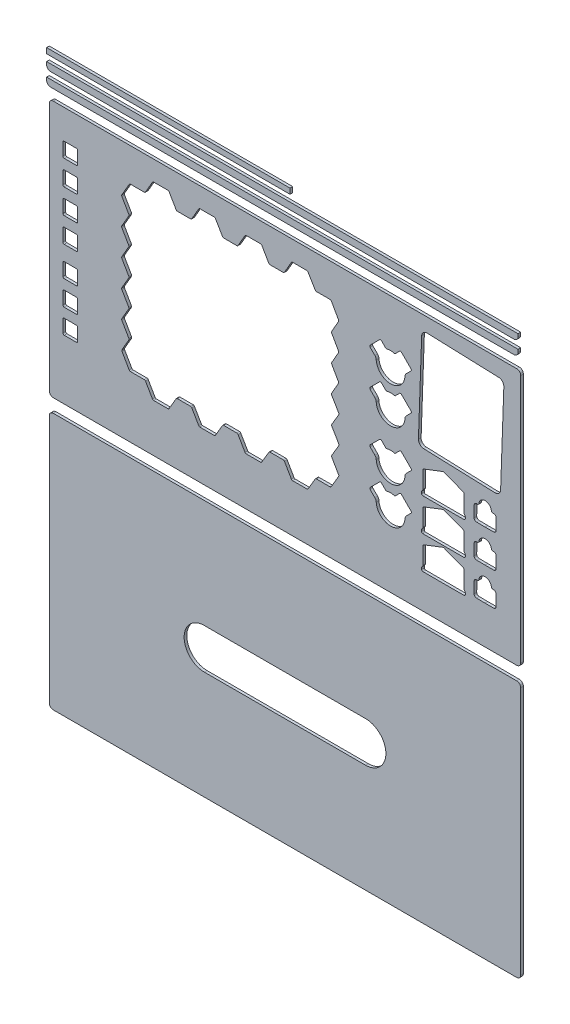
SolidWorks part; units mm, degrees
other "个人版图-顶面"
other "个人版图_长边框"
other "个人版图-长边框2"
other "个人版图-短边框"
other "个人版图-底面"
ref_plane "前视基准面" through (0, 0, 0) normal (0, 0, 1) x (1, 0, 0)
ref_plane "上视基准面" through (0, 0, 0) normal (0, 1, 0) x (1, 0, 0)
ref_plane "右视基准面" through (0, 0, 0) normal (1, 0, 0) x (0, 0, -1)
sketch "草图1"
  line L0 (0, -0.5) -> (340.5, -0.5) construction
  line L1 (0, 0) -> (340, 0) construction
  line L2 (0, 0) -> (0, 180) construction
  line L3 (0, 180) -> (340, 180) construction
  line L4 (340, 0) -> (340, 180) construction
  line L5 (340.5, -0.5) -> (340.5, 180.5) construction
  line L6 (0, 180.5) -> (340.5, 180.5) construction
  line L7 (0, 180.5) -> (0, -0.5) construction
  line L8 (-5, 185.5) -> (-5, -5.5)
  line L9 (-5, -5.5) -> (345.5, -5.5)
  line L10 (345.5, -5.5) -> (345.5, 185.5)
  line L11 (-5, 185.5) -> (345.5, 185.5)
  line L12 (72.0083, 170.7) -> (83.7745, 170.7)
  line L13 (72.0083, 170.7) -> (66.2258, 160.6844)
  line L14 (54.7313, 160.6844) -> (66.2258, 160.6844)
  line L15 (54.7313, 160.6844) -> (48.6498, 150.1509)
  line L16 (48.6498, 150.1509) -> (54.4143, 140.1664)
  line L17 (54.4143, 140.1664) -> (48.6, 130.0957)
  line L18 (48.6, 130.0957) -> (54.3252, 120.1794)
  line L19 (54.3252, 120.1794) -> (48.6138, 110.287)
  line L20 (48.6138, 110.287) -> (54.3978, 100.2686)
  line L21 (54.3978, 100.2686) -> (48.6138, 90.2503)
  line L22 (48.6138, 90.2503) -> (54.3644, 80.2899)
  line L23 (54.3644, 80.2899) -> (48.6422, 70.3787)
  line L24 (48.6422, 70.3787) -> (54.4413, 60.3343)
  line L25 (54.4413, 60.3343) -> (48.7277, 50.4381)
  line L26 (48.7277, 50.4381) -> (54.7313, 40.0396)
  line L27 (54.7313, 40.0396) -> (66.2258, 40.0396)
  line L28 (66.2258, 40.0396) -> (72.0083, 30.0711)
  line L29 (72.0083, 30.0711) -> (83.7745, 30.0711)
  line L30 (83.7745, 30.0711) -> (89.6163, 40.0396)
  line L31 (89.6163, 40.0396) -> (100.6288, 40.0396)
  line L32 (100.6288, 40.0396) -> (106.4113, 30.0711)
  line L33 (106.4113, 30.0711) -> (118.2358, 30.0711)
  line L34 (118.2358, 30.0711) -> (124.0775, 40.0396)
  line L35 (124.0775, 40.0396) -> (135.0409, 40.0396)
  line L36 (135.0409, 40.0396) -> (140.8234, 30.0711)
  line L37 (140.8234, 30.0711) -> (152.6864, 30.0711)
  line L38 (152.6864, 30.0711) -> (158.5281, 40.0396)
  line L39 (158.5281, 40.0396) -> (169.5234, 40.0396)
  line L40 (169.5234, 40.0396) -> (175.3059, 30.0711)
  line L41 (175.3059, 30.0711) -> (187.1478, 30.0711)
  line L42 (187.1478, 30.0711) -> (192.9895, 40.0396)
  line L43 (192.9895, 40.0396) -> (204.3316, 40.0396)
  line L44 (204.3316, 40.0396) -> (210.4252, 50.4381)
  line L45 (210.4252, 50.4381) -> (204.6847, 60.3343)
  line L46 (204.6847, 60.3343) -> (210.5708, 70.3787)
  line L47 (210.5708, 70.3787) -> (204.6847, 80.2899)
  line L48 (204.6847, 80.2899) -> (210.5216, 90.2503)
  line L49 (210.5216, 90.2503) -> (204.5718, 100.2686)
  line L50 (204.5718, 100.2686) -> (210.2931, 110.287)
  line L51 (210.2931, 110.287) -> (204.6847, 120.1794)
  line L52 (204.6847, 120.1794) -> (210.3476, 130.0957)
  line L53 (210.3476, 130.0957) -> (204.6381, 140.1664)
  line L54 (204.6381, 140.1664) -> (210.3476, 150.1641)
  line L55 (210.3476, 150.1641) -> (204.3833, 160.6844)
  line L56 (204.3833, 160.6844) -> (192.9895, 160.6844)
  line L57 (192.9895, 160.6844) -> (187.0413, 170.7)
  line L58 (152.6864, 170.7) -> (158.5281, 160.6844)
  line L59 (158.5281, 160.6844) -> (169.5234, 160.6844)
  line L60 (169.5234, 160.6844) -> (175.3059, 170.7)
  line L61 (118.2358, 170.7) -> (124.0775, 160.6844)
  line L62 (124.0775, 160.6844) -> (135.0409, 160.6844)
  line L63 (135.0409, 160.6844) -> (140.8234, 170.7)
  line L64 (83.7745, 170.7) -> (89.6163, 160.6844)
  line L65 (89.6163, 160.6844) -> (100.6288, 160.6844)
  line L66 (100.6288, 160.6844) -> (106.4113, 170.7)
  line L67 (106.4113, 170.7) -> (118.2358, 170.7)
  line L68 (140.8234, 170.7) -> (152.6864, 170.7)
  line L69 (175.3059, 170.7) -> (187.0413, 170.7)
  line L70 (5.1103, 163.713) -> (16.1103, 163.713)
  line L71 (6.1103, 162.713) -> (15.1103, 162.713) construction
  line L72 (6.1103, 162.713) -> (6.1103, 153.713) construction
  line L73 (6.1103, 153.713) -> (15.1103, 153.713) construction
  line L74 (15.1103, 162.713) -> (15.1103, 153.713) construction
  line L75 (16.1103, 163.713) -> (16.1103, 152.713)
  line L76 (5.1103, 152.713) -> (16.1103, 152.713)
  line L77 (5.1103, 163.713) -> (5.1103, 152.713)
  line L78 (5.1103, 134.263) -> (16.1103, 134.263)
  line L79 (16.1103, 145.263) -> (16.1103, 134.263)
  line L80 (5.1103, 145.263) -> (16.1103, 145.263)
  line L81 (5.1103, 145.263) -> (5.1103, 134.263)
  line L82 (5.1103, 115.813) -> (16.1103, 115.813)
  line L83 (16.1103, 126.813) -> (16.1103, 115.813)
  line L84 (5.1103, 126.813) -> (16.1103, 126.813)
  line L85 (5.1103, 126.813) -> (5.1103, 115.813)
  line L86 (5.1103, 97.363) -> (16.1103, 97.363)
  line L87 (16.1103, 108.363) -> (16.1103, 97.363)
  line L88 (5.1103, 108.363) -> (16.1103, 108.363)
  line L89 (5.1103, 108.363) -> (5.1103, 97.363)
  line L90 (5.1103, 75.2175) -> (16.1103, 75.2175)
  line L91 (16.1103, 86.2175) -> (16.1103, 75.2175)
  line L92 (5.1103, 86.2175) -> (16.1103, 86.2175)
  line L93 (5.1103, 86.2175) -> (5.1103, 75.2175)
  line L94 (5.1103, 56.8589) -> (16.1103, 56.8589)
  line L95 (16.1103, 67.8589) -> (16.1103, 56.8589)
  line L96 (5.1103, 67.8589) -> (16.1103, 67.8589)
  line L97 (5.1103, 67.8589) -> (5.1103, 56.8589)
  line L98 (5.1103, 38.7973) -> (16.1103, 38.7973)
  line L99 (16.1103, 49.7973) -> (16.1103, 38.7973)
  line L100 (5.1103, 49.7973) -> (16.1103, 49.7973)
  line L101 (5.1103, 49.7973) -> (5.1103, 38.7973)
  line L102 (264.6336, 145.4227) -> (256.14, 153.9163)
  line L103 (256.14, 153.9163) -> (251.9519, 149.7283)
  line L104 (245.4671, 149.7283) -> (241.2907, 153.9046)
  line L105 (241.2907, 153.9046) -> (232.8691, 145.483)
  line L106 (232.8691, 145.483) -> (237.0658, 141.2863)
  line L107 (264.6336, 145.4227) -> (260.4972, 141.2863)
  line L108 (264.6336, 81.2459) -> (256.14, 89.7395)
  line L109 (256.14, 89.7395) -> (251.9519, 85.5515)
  line L110 (245.4671, 85.5515) -> (241.2907, 89.7278)
  line L111 (241.2907, 89.7278) -> (232.8691, 81.3062)
  line L112 (232.8691, 81.3062) -> (237.0658, 77.1095)
  line L113 (264.6336, 81.2459) -> (260.4972, 77.1095)
  line L114 (264.6336, 118.3025) -> (256.14, 126.7961)
  line L115 (256.14, 126.7961) -> (251.9519, 122.6081)
  line L116 (245.4671, 122.6081) -> (241.2907, 126.7844)
  line L117 (241.2907, 126.7844) -> (232.8691, 118.3628)
  line L118 (232.8691, 118.3628) -> (237.0658, 114.1661)
  line L119 (264.6336, 118.3025) -> (260.4972, 114.1661)
  line L120 (264.6336, 53.8293) -> (256.14, 62.3229)
  line L121 (256.14, 62.3229) -> (251.9519, 58.1349)
  line L122 (245.4671, 58.1349) -> (241.2907, 62.3112)
  line L123 (241.2907, 62.3112) -> (232.8691, 53.8896)
  line L124 (232.8691, 53.8896) -> (237.0658, 49.6929)
  line L125 (264.6336, 53.8293) -> (260.4972, 49.6929)
  line L126 (272.2895, 20.4596) -> (272.2895, 22.3194) construction
  line L127 (272.2895, 22.3194) -> (273.2488, 23.5312) construction
  line L128 (273.2488, 23.5312) -> (273.2488, 36.9443) construction
  line L129 (273.2488, 36.9443) -> (288.0439, 42.643) construction
  line L130 (272.2895, 20.4596) -> (303.7983, 20.4596) construction
  line L131 (288.0439, 42.643) -> (288.0439, 20.4596) construction
  line L132 (302.839, 36.9443) -> (288.0439, 42.643) construction
  line L133 (302.839, 23.5312) -> (302.839, 36.9443) construction
  line L134 (303.7983, 22.3194) -> (302.839, 23.5312) construction
  line L135 (303.7983, 20.4596) -> (303.7983, 22.3194) construction
  line L136 (303.339, 37.2876) -> (288.0439, 43.1788)
  line L137 (272.7488, 37.2876) -> (288.0439, 43.1788)
  line L138 (272.7488, 23.7052) -> (272.7488, 37.2876)
  line L139 (271.7895, 22.4934) -> (272.7488, 23.7052)
  line L140 (271.7895, 19.9596) -> (271.7895, 22.4934)
  line L141 (271.7895, 19.9596) -> (304.2983, 19.9596)
  line L142 (304.2983, 19.9596) -> (304.2983, 22.4934)
  line L143 (304.2983, 22.4934) -> (303.339, 23.7052)
  line L144 (303.339, 23.7052) -> (303.339, 37.2876)
  line L145 (272.7488, 61.6876) -> (288.0439, 67.5788)
  line L146 (303.339, 61.6876) -> (288.0439, 67.5788)
  line L147 (303.339, 48.1052) -> (303.339, 61.6876)
  line L148 (304.2983, 46.8934) -> (303.339, 48.1052)
  line L149 (304.2983, 44.3596) -> (304.2983, 46.8934)
  line L150 (271.7895, 44.3596) -> (304.2983, 44.3596)
  line L151 (271.7895, 44.3596) -> (271.7895, 46.8934)
  line L152 (271.7895, 46.8934) -> (272.7488, 48.1052)
  line L153 (272.7488, 48.1052) -> (272.7488, 61.6876)
  line L154 (272.7488, 86.0876) -> (288.0439, 91.9788)
  line L155 (303.339, 86.0876) -> (288.0439, 91.9788)
  line L156 (303.339, 72.5052) -> (303.339, 86.0876)
  line L157 (304.2983, 71.2934) -> (303.339, 72.5052)
  line L158 (304.2983, 68.7596) -> (304.2983, 71.2934)
  line L159 (271.7895, 68.7596) -> (304.2983, 68.7596)
  line L160 (271.7895, 68.7596) -> (271.7895, 71.2934)
  line L161 (271.7895, 71.2934) -> (272.7488, 72.5052)
  line L162 (272.7488, 72.5052) -> (272.7488, 86.0876)
  line L163 (319.0697, 88.7733) -> (318.9881, 71.7735) construction
  line L164 (318.9881, 71.7735) -> (325.3925, 71.7735)
  line L165 (327.1925, 73.5735) -> (327.1925, 81.8155)
  line L166 (325.3925, 83.6155) -> (323.6584, 83.6155)
  line L167 (318.9881, 71.7735) -> (312.584, 71.835)
  line L168 (310.8014, 73.6522) -> (310.8806, 81.8939)
  line L169 (312.6978, 83.6765) -> (314.4318, 83.6598)
  line L170 (325.3925, 59.1155) -> (323.6584, 59.1155)
  line L171 (327.1925, 49.0735) -> (327.1925, 57.3155)
  line L172 (318.9881, 47.2735) -> (325.3925, 47.2735)
  line L173 (318.9881, 47.2735) -> (312.584, 47.335)
  line L174 (310.8014, 49.1522) -> (310.8806, 57.3939)
  line L175 (312.6978, 59.1765) -> (314.4318, 59.1598)
  line L176 (325.3925, 34.6155) -> (323.6584, 34.6155)
  line L177 (327.1925, 24.5735) -> (327.1925, 32.8155)
  line L178 (318.9881, 22.7735) -> (325.3925, 22.7735)
  line L179 (318.9881, 22.7735) -> (312.584, 22.835)
  line L180 (310.8014, 24.6522) -> (310.8806, 32.8939)
  line L181 (312.6978, 34.6765) -> (314.4318, 34.6598)
  line L182 (271.9931, 175.2345) -> (333.0932, 173.0732)
  line L183 (333.0932, 173.0732) -> (330.4164, 97.398)
  line L184 (330.4164, 97.398) -> (269.3163, 99.5593)
  line L185 (269.3163, 99.5593) -> (271.9931, 175.2345)
  arc A0 (245.4671, 149.7283) -> (251.9519, 149.7283) centre (248.7095, 139.9876) cw
  arc A1 (237.0658, 141.2863) -> (238.0695, 138.8627) centre (234.6427, 138.8631) cw
  arc A2 (238.0695, 138.8627) -> (259.4313, 138.8627) centre (248.7504, 139.5892) ccw
  arc A3 (260.4972, 141.2863) -> (259.4313, 138.8627) centre (263.0786, 138.7048) ccw
  arc A4 (245.4671, 85.5515) -> (251.9519, 85.5515) centre (248.7095, 75.8108) cw
  arc A5 (237.0658, 77.1095) -> (238.0695, 74.6859) centre (234.6427, 74.6864) cw
  arc A6 (238.0695, 74.6859) -> (259.4313, 74.6859) centre (248.7504, 75.4124) ccw
  arc A7 (260.4972, 77.1095) -> (259.4313, 74.6859) centre (263.0786, 74.5281) ccw
  arc A8 (245.4671, 122.6081) -> (251.9519, 122.6081) centre (248.7095, 112.8674) cw
  arc A9 (237.0658, 114.1661) -> (238.0695, 111.7425) centre (234.6427, 111.743) cw
  arc A10 (238.0695, 111.7425) -> (259.4313, 111.7425) centre (248.7504, 112.469) ccw
  arc A11 (260.4972, 114.1661) -> (259.4313, 111.7425) centre (263.0786, 111.5847) ccw
  arc A12 (245.4671, 58.1349) -> (251.9519, 58.1349) centre (248.7095, 48.3942) cw
  arc A13 (237.0658, 49.6929) -> (238.0695, 47.2693) centre (234.6427, 47.2698) cw
  arc A14 (238.0695, 47.2693) -> (259.4313, 47.2693) centre (248.7504, 47.9958) ccw
  arc A15 (260.4972, 49.6929) -> (259.4313, 47.2693) centre (263.0786, 47.1114) ccw
  arc A16 (314.4318, 83.6598) -> (323.6584, 83.6155) centre (319.0475, 84.1335) cw
  arc A17 (325.3925, 71.7735) -> (327.1925, 73.5735) centre (325.3925, 73.5735) ccw
  arc A18 (327.1925, 81.8155) -> (325.3925, 83.6155) centre (325.3925, 81.8155) ccw
  arc A19 (312.584, 71.835) -> (310.8014, 73.6522) centre (312.6013, 73.635) cw
  arc A20 (310.8806, 81.8939) -> (312.6978, 83.6765) centre (312.6805, 81.8766) cw
  arc A21 (314.4318, 59.1598) -> (323.6584, 59.1155) centre (319.0475, 59.6335) cw
  arc A22 (327.1925, 57.3155) -> (325.3925, 59.1155) centre (325.3925, 57.3155) ccw
  arc A23 (325.3925, 47.2735) -> (327.1925, 49.0735) centre (325.3925, 49.0735) ccw
  arc A24 (312.584, 47.335) -> (310.8014, 49.1522) centre (312.6013, 49.135) cw
  arc A25 (310.8806, 57.3939) -> (312.6978, 59.1765) centre (312.6805, 57.3766) cw
  arc A26 (314.4318, 34.6598) -> (323.6584, 34.6155) centre (319.0475, 35.1335) cw
  arc A27 (327.1925, 32.8155) -> (325.3925, 34.6155) centre (325.3925, 32.8155) ccw
  arc A28 (325.3925, 22.7735) -> (327.1925, 24.5735) centre (325.3925, 24.5735) ccw
  arc A29 (312.584, 22.835) -> (310.8014, 24.6522) centre (312.6013, 24.635) cw
  arc A30 (310.8806, 32.8939) -> (312.6978, 34.6765) centre (312.6805, 32.8766) cw
  point P249 (269.3163, 99.5593)
  dimension "D15" = 1.8
  dimension "D1" = 340
  dimension "D2" = 180
  dimension "D5" = 9.3
  dimension "D6" = 120
  dimension "D7" = 120
  dimension "D8" = 120
  dimension "D9" = 48.6
  dimension "D10" = 9
  dimension "D13" = 0.5
  dimension "D3" = 0.5
  dimension "D4" = 5
  dimension "D11" = 1
  dimension "D12" = 4
  dimension "D14" = 3
  dimension "D16" = 3
extrude "凸台-拉伸1" add sketch "草图1" against normal blind 2
fillet "圆角1" radius 3 4 edges at (-5, -5.5, -1) (-5, 185.5, -1) (345.5, -5.5, -1) (345.5, 185.5, -1)
fillet "圆角2" radius 1 58 edges at (83.7745, 170.7, -1) (89.6163, 160.6844, -1) (100.6288, 160.6844, -1) (106.4113, 170.7, -1) (118.2358, 170.7, -1) (124.0775, 160.6844, -1) (135.0409, 160.6844, -1) (140.8234, 170.7, -1) (152.6864, 170.7, -1) (158.5281, 160.6844, -1) (169.5234, 160.6844, -1) (175.3059, 170.7, -1) (187.0413, 170.7, -1) (192.9895, 160.6844, -1) (204.3833, 160.6844, -1) (210.3476, 150.1641, -1) (204.6381, 140.1664, -1) (210.3476, 130.0957, -1) (204.6847, 120.1794, -1) (210.2931, 110.287, -1) (204.5718, 100.2686, -1) (210.5216, 90.2503, -1) (204.6847, 80.2899, -1) (210.5708, 70.3787, -1) (204.6847, 60.3343, -1) (210.4252, 50.4381, -1) (204.3316, 40.0396, -1) (192.9895, 40.0396, -1) (187.1478, 30.0711, -1) (175.3059, 30.0711, -1) (169.5234, 40.0396, -1) (158.5281, 40.0396, -1) (152.6864, 30.0711, -1) (140.8234, 30.0711, -1) (135.0409, 40.0396, -1) (124.0775, 40.0396, -1) (118.2358, 30.0711, -1) (106.4113, 30.0711, -1) (100.6288, 40.0396, -1) (89.6163, 40.0396, -1) (83.7745, 30.0711, -1) (72.0083, 30.0711, -1) (66.2258, 40.0396, -1) (54.7313, 40.0396, -1) (48.7277, 50.4381, -1) (54.4413, 60.3343, -1) (48.6422, 70.3787, -1) (54.3644, 80.2899, -1) (48.6138, 90.2503, -1) (54.3978, 100.2686, -1) (48.6138, 110.287, -1) (54.3252, 120.1794, -1) (48.6, 130.0957, -1) (54.4143, 140.1664, -1) (48.6498, 150.1509, -1) (54.7313, 160.6844, -1) (72.0083, 170.7, -1) (66.2258, 160.6844, -1)
fillet "圆角3" radius 1 96 edges at (16.1103, 163.713, -1) (5.1103, 152.713, -1) (5.1103, 163.713, -1) (16.1103, 86.2175, -1) (16.1103, 75.2175, -1) (5.1103, 75.2175, -1) (5.1103, 86.2175, -1) (16.1103, 145.263, -1) (16.1103, 134.263, -1) (5.1103, 134.263, -1) (5.1103, 145.263, -1) (16.1103, 126.813, -1) (16.1103, 115.813, -1) (5.1103, 115.813, -1) (5.1103, 126.813, -1) (16.1103, 108.363, -1) (16.1103, 97.363, -1) (5.1103, 97.363, -1) (5.1103, 108.363, -1) (16.1103, 67.8589, -1) (16.1103, 56.8589, -1) (5.1103, 56.8589, -1) (5.1103, 67.8589, -1) (16.1103, 49.7973, -1) (16.1103, 38.7973, -1) (5.1103, 38.7973, -1) (5.1103, 49.7973, -1) (259.4313, 138.8627, -1) (238.0695, 138.8627, -1) (232.8691, 145.483, -1) (241.2907, 153.9046, -1) (245.4671, 149.7283, -1) (251.9519, 149.7283, -1) (256.14, 153.9163, -1) (264.6336, 145.4227, -1) (259.4313, 74.6859, -1) (238.0695, 74.6859, -1) (232.8691, 81.3062, -1) (241.2907, 89.7278, -1) (245.4671, 85.5515, -1) (251.9519, 85.5515, -1) (256.14, 89.7395, -1) (264.6336, 81.2459, -1) (259.4313, 111.7425, -1) (238.0695, 111.7425, -1) (232.8691, 118.3628, -1) (241.2907, 126.7844, -1) (245.4671, 122.6081, -1) (251.9519, 122.6081, -1) (256.14, 126.7961, -1) (264.6336, 118.3025, -1) (259.4313, 47.2693, -1) (238.0695, 47.2693, -1) (232.8691, 53.8896, -1) (241.2907, 62.3112, -1) (245.4671, 58.1349, -1) (251.9519, 58.1349, -1) (256.14, 62.3229, -1) (264.6336, 53.8293, -1) (318.9881, 71.7735, -1) (314.4318, 83.6598, -1) (323.6584, 83.6155, -1) (304.2983, 46.8934, -1) (304.2983, 44.3596, -1) (271.7895, 44.3596, -1) (271.7895, 46.8934, -1) (272.7488, 48.1052, -1) (272.7488, 61.6876, -1) (288.0439, 67.5788, -1) (303.339, 61.6876, -1) (303.339, 48.1052, -1) (304.2983, 22.4934, -1) (304.2983, 19.9596, -1) (271.7895, 19.9596, -1) (271.7895, 22.4934, -1) (272.7488, 23.7052, -1) (272.7488, 37.2876, -1) (288.0439, 43.1788, -1) (303.339, 37.2876, -1) (303.339, 23.7052, -1) (304.2983, 71.2934, -1) (304.2983, 68.7596, -1) (271.7895, 68.7596, -1) (271.7895, 71.2934, -1) (272.7488, 72.5052, -1) (272.7488, 86.0876, -1) (288.0439, 91.9788, -1) (303.339, 86.0876, -1) (303.339, 72.5052, -1) (318.9881, 47.2735, -1) (314.4318, 59.1598, -1) (323.6584, 59.1155, -1) (318.9881, 22.7735, -1) (314.4318, 34.6598, -1) (323.6584, 34.6155, -1) (16.1103, 152.713, -1)
sketch "草图3" plane through (0, 0, 0) normal (0, 0, 1) x (1, 0, 0)
  line L0 (-5, 182.5) -> (-5, -2.5) construction
  line L1 (-5, 195.5) -> (345.5, 195.5)
  line L2 (-5, 195.5) -> (-5, 200.5)
  line L3 (-5, 200.5) -> (345.5, 200.5)
  line L4 (345.5, 195.5) -> (345.5, 200.5)
  line L5 (345.5, -2.5) -> (345.5, 182.5) construction
  line L6 (342.5, 185.5) -> (-2, 185.5) construction
  dimension "D1" = 5
  dimension "D2" = 10
extrude "凸台-拉伸2" add sketch "草图3" along normal blind 2 separate body
fillet "圆角4" radius 3 2 edges at (345.5, 195.5, 1) (-5, 195.5, 1)
pattern_linear "阵列(线性)1" count 2 spacing 10 along (0, 1, 0) of bodies 107
sketch "草图6" plane through (0, 0, 0) normal (0, 0, 1) x (1, 0, 0)
  line L0 (345.5, 210.5) -> (-5, 210.5) construction
  line L1 (-5, 215.5) -> (176, 215.5)
  line L2 (-5, 215.5) -> (-5, 219.5)
  line L3 (-5, 219.5) -> (176, 219.5)
  line L4 (176, 215.5) -> (176, 219.5)
  dimension "D1" = 5
  dimension "D2" = 4
  dimension "D3" = 181
extrude "凸台-拉伸4" add sketch "草图6" along normal blind 2 separate body
sketch "草图7" plane through (0, 0, 0) normal (0, 0, 1) x (1, 0, 0)
  line L0 (-5, 182.5) -> (-5, -2.5) construction
  line L1 (-5, -15.5) -> (345.5, -15.5)
  line L2 (-5, -15.5) -> (-5, -206.5)
  line L3 (-5, -206.5) -> (345.5, -206.5)
  line L4 (345.5, -15.5) -> (345.5, -206.5)
  line L5 (-2, -5.5) -> (342.5, -5.5) construction
  dimension "D1" = 350.5
  dimension "D2" = 191
  dimension "D3" = 10
extrude "凸台-拉伸5" add sketch "草图7" against normal blind 2 separate body
fillet "圆角5" radius 3 4 edges at (-5, -206.5, -1) (345.5, -206.5, -1) (-5, -15.5, -1) (345.5, -15.5, -1)
sketch "草图8" plane through (0, 0, 0) normal (0, 0, 1) x (1, 0, 0)
  line L0 (110.25, -111) -> (230.25, -111) construction
  line L1 (110.25, -96) -> (230.25, -96)
  line L2 (110.25, -126) -> (230.25, -126)
  line L3 (110.25, -111) -> (110.25, -15.5) construction
  line L4 (342.5, -15.5) -> (-2, -15.5) construction
  line L5 (110.25, -111) -> (110.25, -206.5) construction
  line L6 (-2, -206.5) -> (342.5, -206.5) construction
  line L7 (110.25, -111) -> (-5, -111) construction
  line L8 (-5, -18.5) -> (-5, -203.5) construction
  line L9 (230.25, -111) -> (345.5, -111) construction
  line L10 (345.5, -203.5) -> (345.5, -18.5) construction
  arc A0 (110.25, -96) -> (110.25, -126) centre (110.25, -111) ccw
  arc A1 (230.25, -126) -> (230.25, -96) centre (230.25, -111) ccw
  point P2 (170.25, -111)
  dimension "D1" = 15
  dimension "D2" = 120
extrude "切除-拉伸1" cut sketch "草图8" against normal blind 2
fillet "圆角6" radius 4 4 edges at (333.0932, 173.0732, -1) (330.4164, 97.398, -1) (271.9931, 175.2345, -1) (269.3163, 99.5593, -1)
other "保存实体1"
